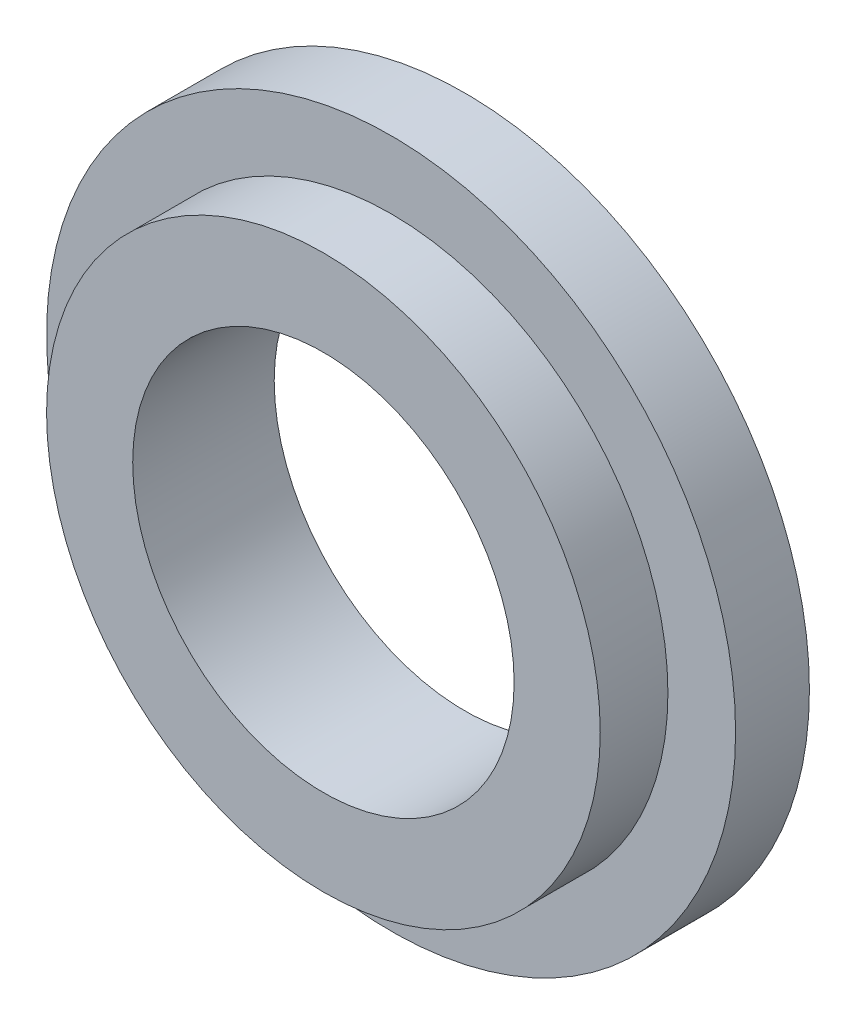
SolidWorks part; units mm, degrees
ref_plane "Plan de face" through (0, 0, 0) normal (0, 0, 1) x (1, 0, 0)
ref_plane "Plan de dessus" through (0, 0, 0) normal (0, 1, 0) x (1, 0, 0)
ref_plane "Plan de droite" through (0, 0, 0) normal (1, 0, 0) x (0, 0, -1)
sketch "Esquisse1" plane through (0, 0, 0) normal (0, 0, 1) x (1, 0, 0)
  circle A0 centre (0, 0) radius 14
  dimension "D1" = 28
extrude "Boss.-Extru.1" add sketch "Esquisse1" along normal blind 3
sketch "Esquisse2" plane through (0, 0, 3) normal (0, 0, 1) x (1, 0, 0)
  circle A0 centre (0, 0) radius 11.25
  dimension "D1" = 22.5
extrude "Boss.-Extru.2" add sketch "Esquisse2" along normal blind 2.75
sketch "Esquisse3" plane through (0, 0, 5.75) normal (0, 0, 1) x (1, 0, 0)
  circle A0 centre (0, 0) radius 7.75
  dimension "D1" = 15.5
extrude "Enlèv. mat.-Extru.1" cut sketch "Esquisse3" against normal up to surface (5.75 mm away) up to face at (14, 0, 0)
